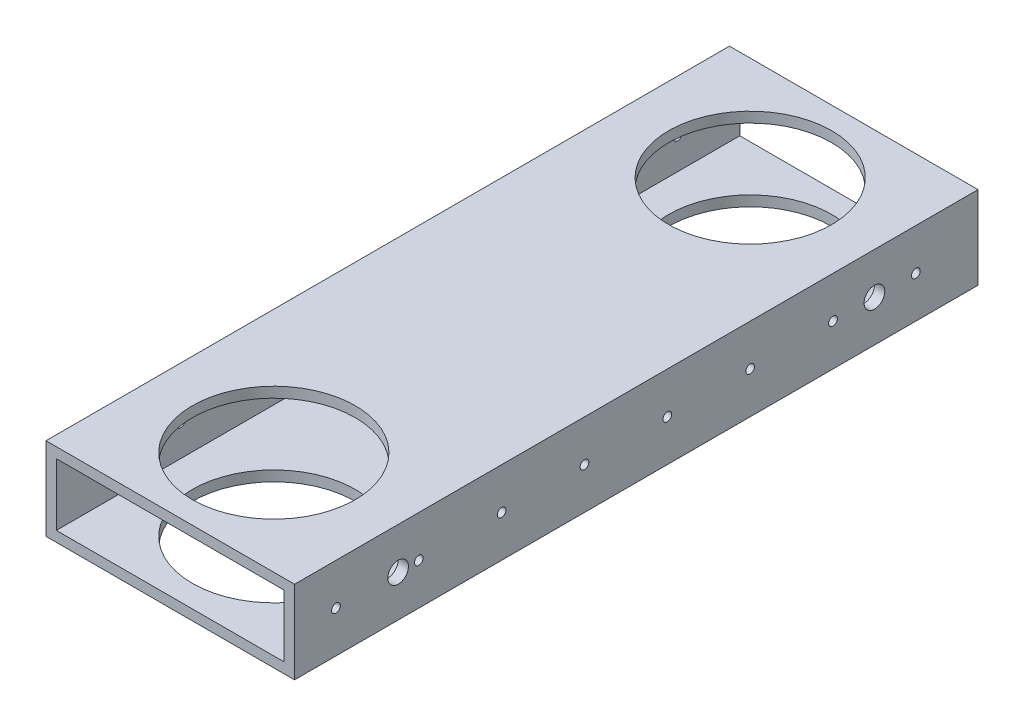
SolidWorks part; units mm, degrees
ref_plane "Front" through (0, 0, 0) normal (0, 0, 1) x (1, 0, 0)
ref_plane "Top" through (0, 0, 0) normal (0, 1, 0) x (1, 0, 0)
ref_plane "Right" through (0, 0, 0) normal (1, 0, 0) x (0, 0, -1)
sketch "Sketch2" plane through (0, 0, 0) normal (0, 0, 1) x (1, 0, 0)
  line L1 (-38.1, -12.7) -> (38.1, -12.7)
  line L2 (-38.1, -12.7) -> (-38.1, 12.7)
  line L3 (-38.1, 12.7) -> (38.1, 12.7)
  line L4 (38.1, -12.7) -> (38.1, 12.7)
  line L5 (-38.1, -12.7) -> (38.1, 12.7) construction
  line L6 (-38.1, 12.7) -> (38.1, -12.7) construction
  point P0 (0, 0)
  dimension "D1" = 25.4
  dimension "D2" = 76.2
extrude "Extrude-Thin1" add sketch "Sketch2" along normal blind 209.55 thin thin type one direction reverse wall 3.175
sketch "Sketch3" plane through (0, 12.7, 0) normal (0, 1, 0) x (1, 0, 0)
  line L0 (-38.1, -209.55) -> (-38.1, -177.8) construction
  line L1 (-38.1, -209.55) -> (-38.1, 0) construction
  line L2 (-38.1, -177.8) -> (38.1, -177.8) construction
  line L3 (38.1, -209.55) -> (38.1, 0) construction
  line L4 (38.1, -104.775) -> (-38.1, -104.775) construction
  circle A0 centre (0, -177.8) radius 24.972
  circle A1 centre (0, -31.75) radius 24.972
  point P14 (-38.1, -174.625)
  dimension "D2" = 49.944
  dimension "D1" = 146.05
extrude "Cut-Extrude1" cut sketch "Sketch3" against normal through all
sketch "Sketch4" plane through (38.1, 0, 0) normal (1, 0, 0) x (0, 0, -1)
  line L0 (-209.55, 0) -> (-196.85, 0) construction
  line L1 (-209.55, -12.7) -> (-209.55, 12.7) construction
  circle A0 centre (-196.85, 0) radius 1.3335
  dimension "D1" = 2.667
  dimension "D2" = 12.7
extrude "Cut-Extrude2" cut sketch "Sketch4" against normal through all
pattern_linear "LPattern1" count 9 spacing 25.4 along (0, 0, -1) of "Cut-Extrude2"
sketch "Sketch5" plane through (38.1, 0, 0) normal (1, 0, 0) x (0, 0, -1)
  line L0 (0, 0) -> (-31.75, 0) construction
  line L1 (0, -12.7) -> (0, 12.7) construction
  line L2 (-104.775, 12.7) -> (-104.775, -12.7) construction
  line L3 (-209.55, 12.7) -> (0, 12.7) construction
  line L4 (-209.55, -12.7) -> (0, -12.7) construction
  line L5 (-6.778, 12.7) -> (-56.722, 12.7) construction
  line L6 (-6.778, 12.7) -> (-56.722, 12.7) construction
  line L7 (-31.75, 12.7) -> (-31.75, 0) construction
  circle A0 centre (-31.75, 0) radius 3.175
  circle A1 centre (-177.8, 0) radius 3.175
  dimension "D1" = 6.35
extrude "Cut-Extrude3" cut sketch "Sketch5" against normal through all
